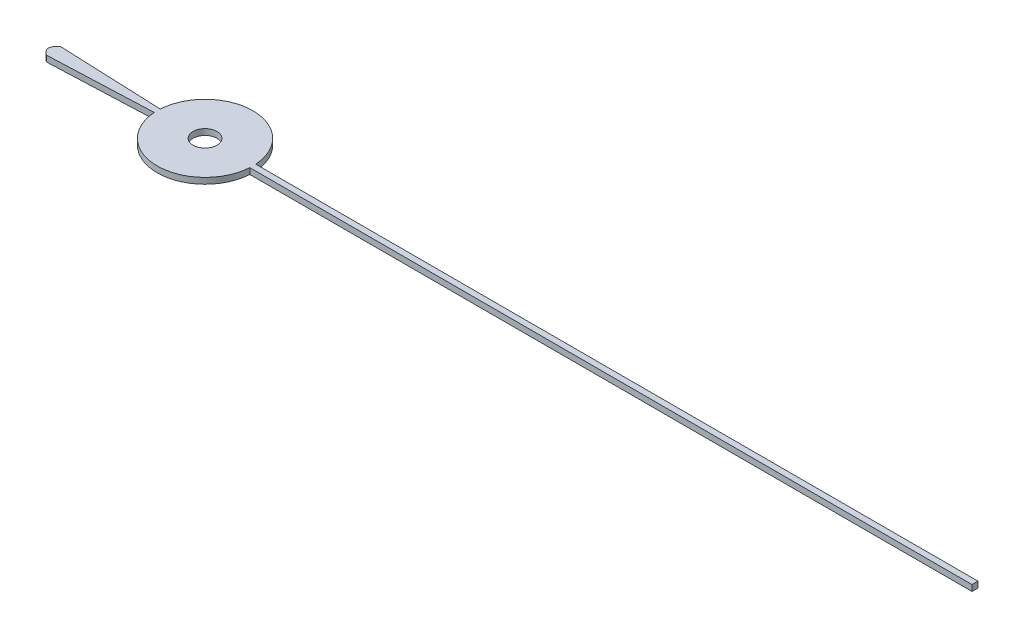
SolidWorks part; units mm, degrees
ref_plane "Front Plane" through (0, 0, 0) normal (0, 0, 1) x (1, 0, 0)
ref_plane "Top Plane" through (0, 0, 0) normal (0, 1, 0) x (1, 0, 0)
ref_plane "Right Plane" through (0, 0, 0) normal (1, 0, 0) x (0, 0, -1)
sketch "Sketch1" plane through (0, 0, 0) normal (0, 1, 0) x (1, 0, 0)
  line L0 (0, 0) -> (4, 0) construction
  line L1 (0, 0) -> (-0.3417, 0) construction
  line L2 (4, -0.25) -> (64.4873, -0.25)
  line L3 (4, 0.25) -> (64.4873, 0.25)
  line L4 (64.4873, -0.25) -> (64.4873, 0.25)
  line L5 (-13.1058, 0) -> (-0.1709, 0) construction
  line L6 (-12.6777, 0.6063) -> (-4, 0.25)
  line L7 (-12.6777, -0.6063) -> (-4, -0.25)
  circle A0 centre (0, 0) radius 4.0078
  spline S0 degree 2 poles (-12.6777, -0.6063) (-13.5338, 0) (-12.6777, 0.6063) knots 0 0 0 1 1 1
extrude "Boss-Extrude2" add sketch "Sketch1" along normal blind 0.5
sketch "Sketch3" plane through (0, 0.5, 0) normal (0, 1, 0) x (1, 0, 0)
  circle A0 centre (0, 0) radius 1
extrude "Cut-Extrude2" cut sketch "Sketch3" against normal through all
